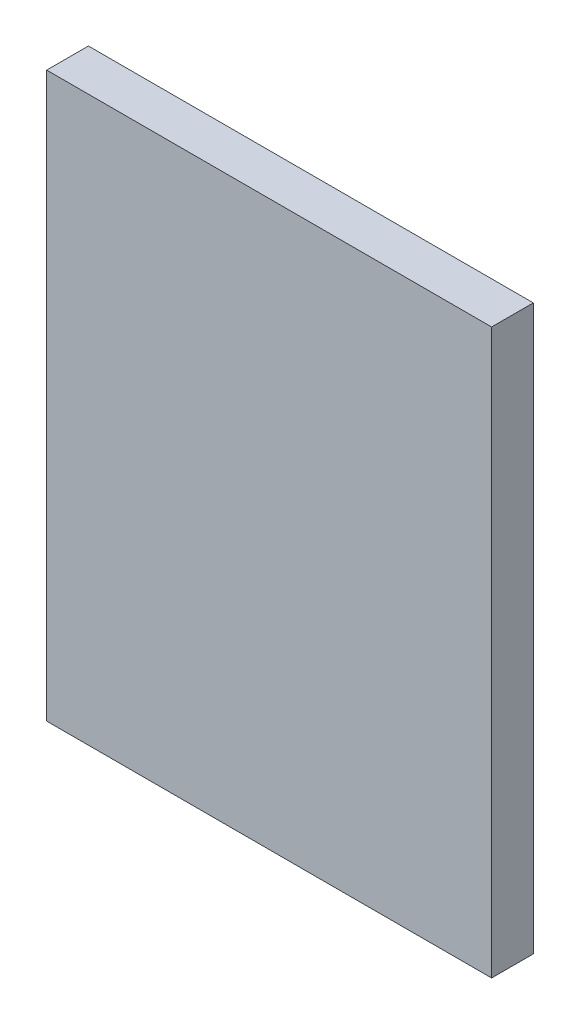
SolidWorks part; units mm, degrees
ref_plane "Front Plane" through (0, 0, 0) normal (0, 0, 1) x (1, 0, 0)
ref_plane "Top Plane" through (0, 0, 0) normal (0, 1, 0) x (1, 0, 0)
ref_plane "Right Plane" through (0, 0, 0) normal (1, 0, 0) x (0, 0, -1)
sketch "Sketch1" plane through (0, 0, 0) normal (0, 0, 1) x (1, 0, 0)
  line L1 (0, 0) -> (32, 0)
  line L2 (0, 0) -> (0, 40.55)
  line L3 (0, 40.55) -> (32, 40.55)
  line L4 (32, 0) -> (32, 40.55)
  dimension "D1" = 40.55
  dimension "D2" = 32
extrude "Boss-Extrude1" add sketch "Sketch1" along normal blind 3
